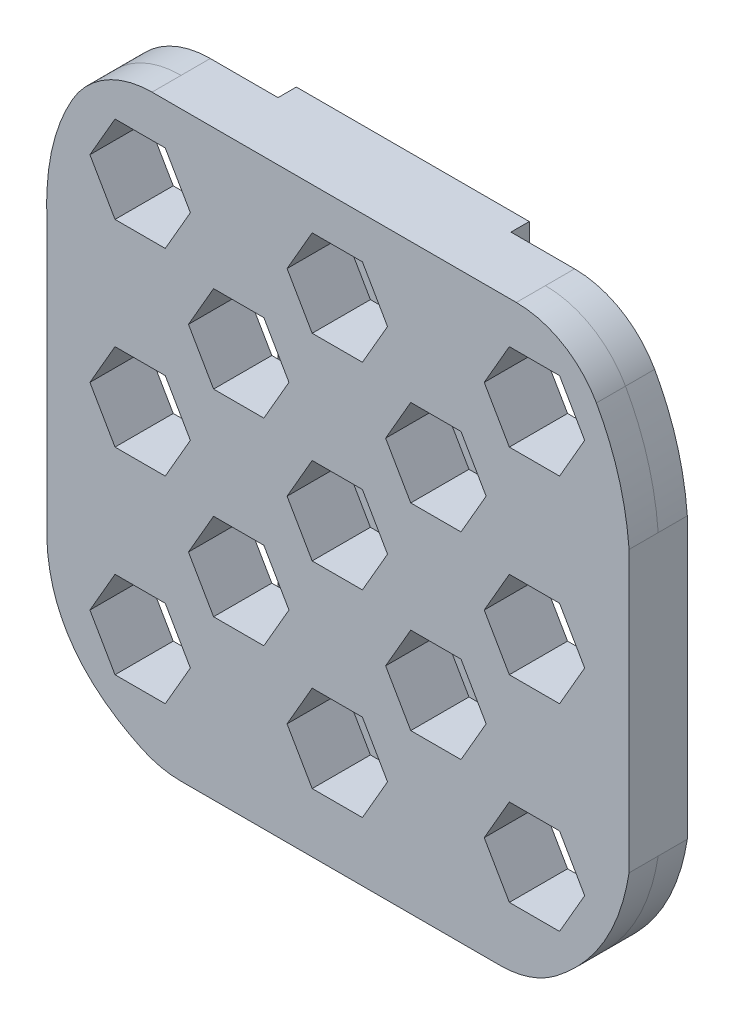
SolidWorks part; units mm, degrees
ref_plane "Front Plane" through (0, 0, 0) normal (0, 0, 1) x (1, 0, 0)
ref_plane "Top Plane" through (0, 0, 0) normal (0, 1, 0) x (1, 0, 0)
ref_plane "Right Plane" through (0, 0, 0) normal (1, 0, 0) x (0, 0, -1)
sketch "Sketch1" plane through (0, 0, 0) normal (0, 0, 1) x (1, 0, 0)
  line L1 (12.5861, 0) -> (52.3416, 0)
  line L2 (0, 15.7832) -> (0, 46.322)
  line L3 (6.8272, 63.5) -> (56.3058, 63.5)
  line L4 (63.5, 15.7832) -> (63.5, 46.322)
  spline S0 degree 2 poles (0, 15.7832) (0.3049, 4.6516) (12.5861, 0) knots 0 0 0 1 1 1
  spline S1 degree 2 poles (63.5, 15.7832) (61.8182, 5.1639) (52.3416, 0) knots 0 0 0 1 1 1
  spline S2 degree 2 poles (0, 46.322) (-0.2991, 56.8687) (6.8272, 63.5) knots 0 0 0 1 1 1
  spline S3 degree 2 poles (63.5, 46.322) (62.736, 56.1525) (56.3058, 63.5) knots 0 0 0 1 1 1
  point P1 (3.5727, 59.712)
  point P2 (60.95, 56.3748)
extrude "Boss-Extrude1" add sketch "Sketch1" along normal blind 3.175
sketch "Sketch2" plane through (0, 0, 0) normal (0, 0, -1) x (-1, 0, 0)
  line L0 (-31.5665, 63.5) -> (-31.5665, 0)
  line L1 (-56.3058, 63.5) -> (-6.8272, 63.5) construction
  line L2 (-12.5861, 0) -> (-52.3416, 0) construction
  line L3 (-18.8665, 63.5) -> (-18.8665, 0)
  line L4 (-44.2665, 0) -> (-44.2665, 63.5)
  line L5 (-44.2665, 63.5) -> (-18.8665, 63.5)
  line L6 (-44.2665, 0) -> (-18.8665, 0)
  line M7 (-6.8272, 63.5) -> (-56.3058, 63.5)
  line M11 (-52.3416, 0) -> (-12.5861, 0)
  dimension "D1" = 25.4
  dimension "D2" = 12.7
sketch "Sketch3" plane through (0, 0, 3.175) normal (0, 0, 1) x (1, 0, 0)
  line L4 (12.5861, 0) -> (52.3416, 0)
  line L5 (63.5, 15.7832) -> (63.5, 46.322)
  line L6 (56.3058, 63.5) -> (6.8272, 63.5)
  line L7 (0, 46.322) -> (0, 15.7832)
  line L8 (12.5861, 0) -> (52.3416, 0)
  line L9 (63.5, 15.7832) -> (63.5, 46.322)
  line L10 (56.3058, 63.5) -> (6.8272, 63.5)
  line L11 (0, 46.322) -> (0, 15.7832)
  parabola Q4 (0, 15.7832) -> (12.5861, 0) focus (8.2347, 11.8945) apex (1.8588, 8.4447)
  parabola Q5 (52.3416, 0) -> (63.5, 15.7832) focus (51.8801, 12.2331) apex (59.9231, 6.6039)
  parabola Q6 (63.5, 46.322) -> (56.3058, 63.5) focus (48.3039, 50.3303) apex (61.1381, 55.9548)
  parabola Q7 (6.8272, 63.5) -> (0, 46.322) focus (11.3612, 53.1625) apex (2.4624, 57.855)
  parabola Q8 (0, 15.7832) -> (12.5861, 0) focus (8.2347, 11.8945) apex (1.8588, 8.4447)
  parabola Q9 (52.3416, 0) -> (63.5, 15.7832) focus (51.8801, 12.2331) apex (59.9231, 6.6039)
  parabola Q10 (63.5, 46.322) -> (56.3058, 63.5) focus (48.3039, 50.3303) apex (61.1381, 55.9548)
  parabola Q11 (6.8272, 63.5) -> (0, 46.322) focus (11.3612, 53.1625) apex (2.4624, 57.855)
  dimension "D1" = 0
extrude "Boss-Extrude2" add sketch "Sketch3" along normal blind 3.175
sketch "Sketch4" plane through (0, 0, 6.35) normal (0, 0, 1) x (1, 0, 0)
  line L0 (56.3058, 63.5) -> (6.8272, 63.5) construction
  line L1 (12.9192, 49.4576) -> (15.6579, 54.2012)
  line L2 (15.6579, 54.2012) -> (12.9192, 58.9448)
  line L3 (12.9192, 58.9448) -> (7.4418, 58.9448)
  line L4 (7.4418, 58.9448) -> (4.7031, 54.2012)
  line L5 (4.7031, 54.2012) -> (7.4418, 49.4576)
  line L6 (7.4418, 49.4576) -> (12.9192, 49.4576)
  line L7 (34.4192, 49.4576) -> (37.1579, 54.2012)
  line L8 (37.1579, 54.2012) -> (34.4192, 58.9448)
  line L9 (34.4192, 58.9448) -> (28.9418, 58.9448)
  line L10 (28.9418, 58.9448) -> (26.2031, 54.2012)
  line L11 (26.2031, 54.2012) -> (28.9418, 49.4576)
  line L12 (28.9418, 49.4576) -> (34.4192, 49.4576)
  line L13 (55.9192, 49.4576) -> (58.6579, 54.2012)
  line L14 (58.6579, 54.2012) -> (55.9192, 58.9448)
  line L15 (55.9192, 58.9448) -> (50.4418, 58.9448)
  line L16 (50.4418, 58.9448) -> (47.7031, 54.2012)
  line L17 (47.7031, 54.2012) -> (50.4418, 49.4576)
  line L18 (50.4418, 49.4576) -> (55.9192, 49.4576)
  line L19 (34.4192, 27.9576) -> (37.1579, 32.7012)
  line L20 (37.1579, 32.7012) -> (34.4192, 37.4448)
  line L21 (34.4192, 37.4448) -> (28.9418, 37.4448)
  line L22 (28.9418, 37.4448) -> (26.2031, 32.7012)
  line L23 (26.2031, 32.7012) -> (28.9418, 27.9576)
  line L24 (28.9418, 27.9576) -> (34.4192, 27.9576)
  line L25 (55.9192, 27.9576) -> (58.6579, 32.7012)
  line L26 (58.6579, 32.7012) -> (55.9192, 37.4448)
  line L27 (55.9192, 37.4448) -> (50.4418, 37.4448)
  line L28 (50.4418, 37.4448) -> (47.7031, 32.7012)
  line L29 (47.7031, 32.7012) -> (50.4418, 27.9576)
  line L30 (50.4418, 27.9576) -> (55.9192, 27.9576)
  line L31 (34.4192, 6.4576) -> (37.1579, 11.2012)
  line L32 (37.1579, 11.2012) -> (34.4192, 15.9448)
  line L33 (34.4192, 15.9448) -> (28.9418, 15.9448)
  line L34 (28.9418, 15.9448) -> (26.2031, 11.2012)
  line L35 (26.2031, 11.2012) -> (28.9418, 6.4576)
  line L36 (28.9418, 6.4576) -> (34.4192, 6.4576)
  line L37 (55.9192, 6.4576) -> (58.6579, 11.2012)
  line L38 (58.6579, 11.2012) -> (55.9192, 15.9448)
  line L39 (55.9192, 15.9448) -> (50.4418, 15.9448)
  line L40 (50.4418, 15.9448) -> (47.7031, 11.2012)
  line L41 (47.7031, 11.2012) -> (50.4418, 6.4576)
  line L42 (50.4418, 6.4576) -> (55.9192, 6.4576)
  line L43 (12.9192, 27.9576) -> (15.6579, 32.7012)
  line L44 (15.6579, 32.7012) -> (12.9192, 37.4448)
  line L45 (12.9192, 37.4448) -> (7.4418, 37.4448)
  line L46 (7.4418, 37.4448) -> (4.7031, 32.7012)
  line L47 (4.7031, 32.7012) -> (7.4418, 27.9576)
  line L48 (7.4418, 27.9576) -> (12.9192, 27.9576)
  line L49 (12.9192, 6.4576) -> (15.6579, 11.2012)
  line L50 (15.6579, 11.2012) -> (12.9192, 15.9448)
  line L51 (12.9192, 15.9448) -> (7.4418, 15.9448)
  line L52 (7.4418, 15.9448) -> (4.7031, 11.2012)
  line L53 (4.7031, 11.2012) -> (7.4418, 6.4576)
  line L54 (7.4418, 6.4576) -> (12.9192, 6.4576)
  line L55 (15.6579, 54.2012) -> (26.2031, 54.2012)
  line L56 (12.9192, 49.4576) -> (12.9192, 37.4448)
  line L57 (45.1705, 38.8085) -> (47.9105, 43.5543)
  line L58 (23.6705, 38.8085) -> (26.4105, 43.5543)
  line L59 (26.4105, 43.5543) -> (23.6705, 48.3001)
  line L60 (23.6705, 48.3001) -> (18.1905, 48.3001)
  line L61 (18.1905, 48.3001) -> (15.4505, 43.5543)
  line L62 (15.4505, 43.5543) -> (18.1905, 38.8085)
  line L63 (18.1905, 38.8085) -> (23.6705, 38.8085)
  line L64 (47.9105, 43.5543) -> (45.1705, 48.3001)
  line L65 (45.1705, 48.3001) -> (39.6905, 48.3001)
  line L66 (39.6905, 48.3001) -> (36.9505, 43.5543)
  line L67 (36.9505, 43.5543) -> (39.6905, 38.8085)
  line L68 (39.6905, 38.8085) -> (45.1705, 38.8085)
  line L69 (45.1705, 17.3085) -> (47.9105, 22.0543)
  line L70 (47.9105, 22.0543) -> (45.1705, 26.8001)
  line L71 (45.1705, 26.8001) -> (39.6905, 26.8001)
  line L72 (39.6905, 26.8001) -> (36.9505, 22.0543)
  line L73 (36.9505, 22.0543) -> (39.6905, 17.3085)
  line L74 (39.6905, 17.3085) -> (45.1705, 17.3085)
  line L75 (23.6705, 17.3085) -> (26.4105, 22.0543)
  line L76 (26.4105, 22.0543) -> (23.6705, 26.8001)
  line L77 (23.6705, 26.8001) -> (18.1905, 26.8001)
  line L78 (18.1905, 26.8001) -> (15.4505, 22.0543)
  line L79 (15.4505, 22.0543) -> (18.1905, 17.3085)
  line L80 (18.1905, 17.3085) -> (23.6705, 17.3085)
  circle A0 centre (10.1805, 54.2012) radius 4.7436 construction
  circle A1 centre (20.9305, 43.5543) radius 4.7458 construction
  dimension "D1" = 0
  dimension "D4" = 0
  dimension "D5" = 5.48
  dimension "D2" = 3
  dimension "D3" = 3
  dimension "D6" = 2
  dimension "D7" = 2
extrude "Boss-Extrude3" add sketch "Sketch2" along normal blind 2 contours L3 L0 M7 M11 | L4 L0 M11 M7
extrude "Cut-Extrude1" cut sketch "Sketch4" against normal blind 6.35 contours L17 L18 L13 L14 L15 L16 | L67 L68 L57 L64 L65 L66 | L29 L30 L25 L26 L27 L28 | L73 L74 L69 L70 L71 L72 | L41 L42 L37 L38 L39 L40 | L35 L36 L31 L32 L33 L34 | L23 L24 L19 L20 L21 L22 | L11 L12 L7 L8 L9 L10 | L62 L63 L58 L59 L60 L61 | L5 L6 L1 L2 L3 L4 | L47 L48 L43 L44 L45 L46 | L79 L80 L75 L76 L77 L78 | L53 L54 L49 L50 L51 L52
fillet "Fillet1" radius 10 8 edges at (56.3058, 63.5, 4.7625) (52.3416, 0, 1.5875) (12.5861, 0, 1.5875) (6.8272, 63.5, 4.7625) (56.3058, 63.5, 1.5875) (52.3416, 0, 4.7625) (12.5861, 0, 4.7625) (6.8272, 63.5, 1.5875)
